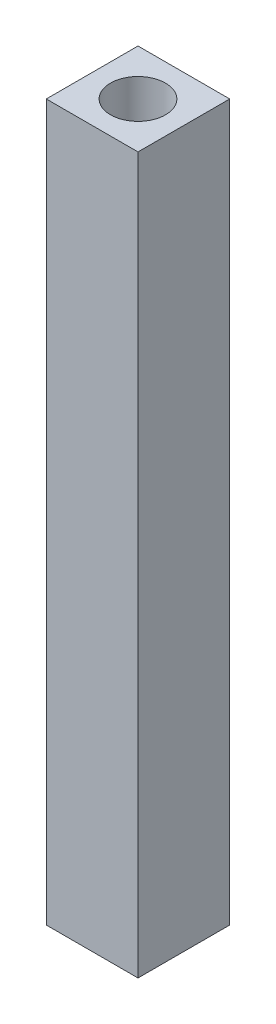
SolidWorks part; units mm, degrees
ref_plane "Front Plane" through (0, 0, 0) normal (0, 0, 1) x (1, 0, 0)
ref_plane "Top Plane" through (0, 0, 0) normal (0, 1, 0) x (1, 0, 0)
ref_plane "Right Plane" through (0, 0, 0) normal (1, 0, 0) x (0, 0, -1)
sketch "Sketch1" plane through (0, 0, 0) normal (0, 1, 0) x (1, 0, 0)
  line L1 (-2.5, -2.5) -> (2.5, -2.5)
  line L2 (-2.5, -2.5) -> (-2.5, 2.5)
  line L3 (-2.5, 2.5) -> (2.5, 2.5)
  line L4 (2.5, -2.5) -> (2.5, 2.5)
  line L5 (-2.5, -2.5) -> (2.5, 2.5) construction
  line L6 (-2.5, 2.5) -> (2.5, -2.5) construction
  circle A0 centre (0, 0) radius 1.5
  dimension "D1" = 3
  dimension "D2" = 2.5
extrude "Boss-Extrude1" add sketch "Sketch1" along normal blind 39
